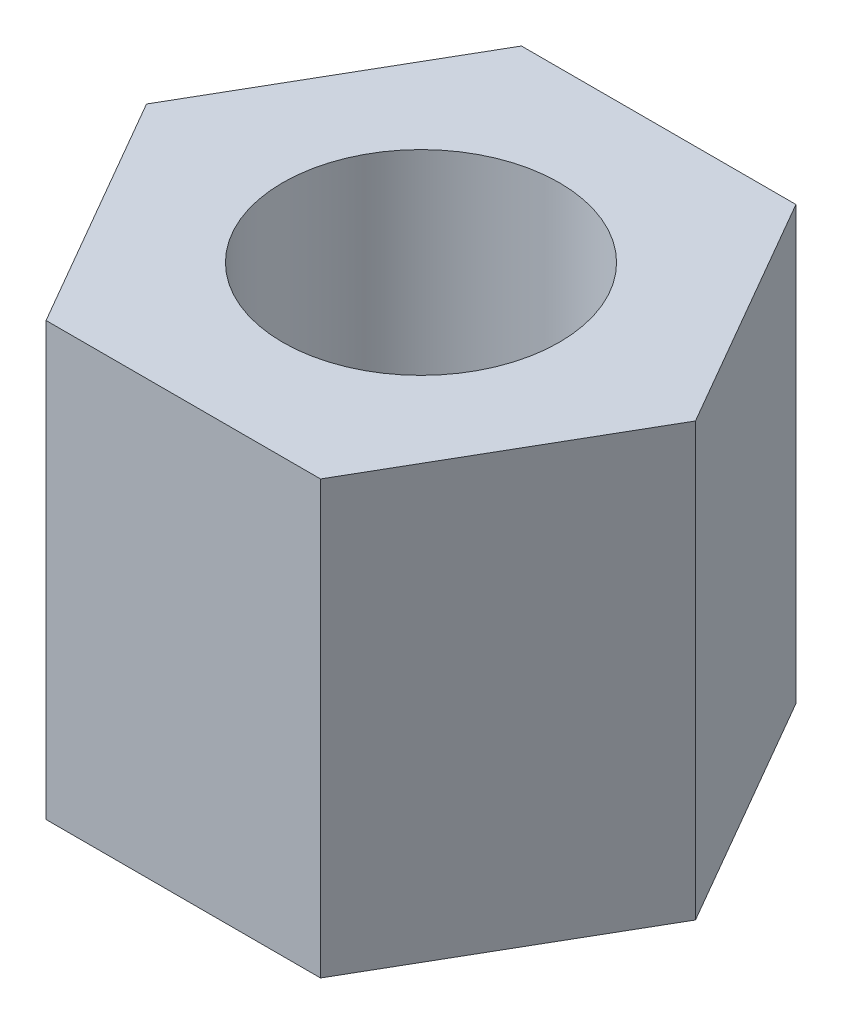
SolidWorks part; units mm, degrees
material "尼龙 101"
ref_plane "前视基准面" through (0, 0, 0) normal (0, 0, 1) x (1, 0, 0)
ref_plane "上视基准面" through (0, 0, 0) normal (0, 1, 0) x (1, 0, 0)
ref_plane "右视基准面" through (0, 0, 0) normal (1, 0, 0) x (0, 0, -1)
sketch "草图1" plane through (0, 0, 0) normal (0, 1, 0) x (1, 0, 0)
  line L1 (3.1754, 0) -> (1.5877, 2.75)
  line L2 (1.5877, 2.75) -> (-1.5877, 2.75)
  line L3 (-1.5877, 2.75) -> (-3.1754, 0)
  line L4 (-3.1754, 0) -> (-1.5877, -2.75)
  line L5 (-1.5877, -2.75) -> (1.5877, -2.75)
  line L6 (1.5877, -2.75) -> (3.1754, 0)
  circle A0 centre (0, 0) radius 2.75 construction
  dimension "D1" = 5.5
extrude "凸台-拉伸1" add sketch "草图1" along normal blind 5
sketch "草图2" plane through (0, 5, 0) normal (0, 1, 0) x (1, 0, 0)
  circle A0 centre (0, 0) radius 1.6
  dimension "D1" = 3.2
extrude "切除-拉伸1" cut sketch "草图2" against normal through all
